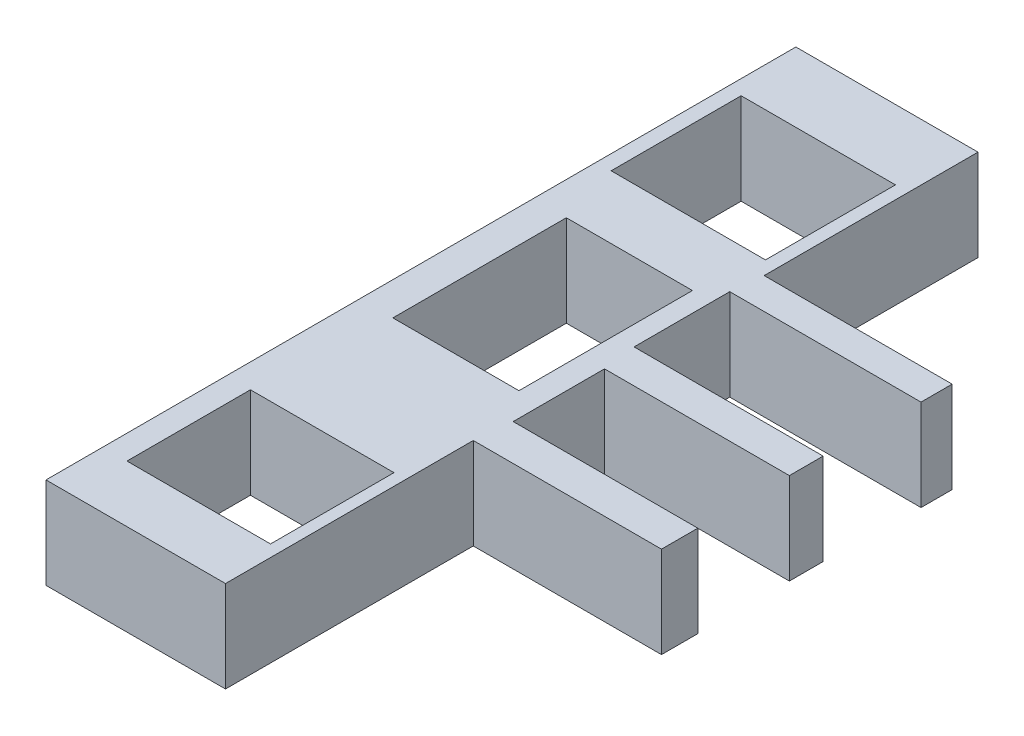
SolidWorks part; units mm, degrees
ref_plane "Front Plane" through (0, 0, 0) normal (0, 0, 1) x (1, 0, 0)
ref_plane "Top Plane" through (0, 0, 0) normal (0, 1, 0) x (1, 0, 0)
ref_plane "Right Plane" through (0, 0, 0) normal (1, 0, 0) x (0, 0, -1)
sketch "Sketch2" plane through (0, 0, 0) normal (0, 1, 0) x (1, 0, 0)
  line L0 (-27.9086, 57.4835) -> (-27.9086, -57.4249)
  line L1 (-27.9086, -57.4249) -> (-0.4053, -57.4249)
  line L2 (-0.4053, -57.4249) -> (-0.4053, -19.4557)
  line L3 (-0.4053, -19.4557) -> (28.4376, -19.4557)
  line L4 (28.4376, -19.4557) -> (28.4376, -13.8879)
  line L5 (28.4376, -13.8879) -> (0.1436, -13.8879)
  line L6 (0.1436, -13.8879) -> (0.1436, 0.106)
  line L7 (0.1436, 0.106) -> (28.4721, 0.106)
  line L8 (28.4721, 0.106) -> (28.4721, 5.2825)
  line L9 (28.4721, 5.2825) -> (-0.5019, 5.2825)
  line L10 (-0.5019, 5.2825) -> (-0.5019, 19.9459)
  line L11 (-0.5019, 19.9459) -> (28.8074, 19.9459)
  line L12 (28.8074, 19.9459) -> (28.8074, 24.7164)
  line L13 (28.8074, 24.7164) -> (0, 24.7164)
  line L14 (0, 24.7164) -> (0, 57.4835)
  line L15 (0, 57.4835) -> (-27.9086, 57.4835)
  line L17 (-25.6311, 26.8967) -> (-1.9799, 26.8967)
  line L18 (-25.6311, 26.8967) -> (-25.6311, 46.817)
  line L19 (-25.6311, 46.817) -> (-1.9799, 46.817)
  line L20 (-1.9799, 26.8967) -> (-1.9799, 46.817)
  line L21 (-22.833, 17.2364) -> (-3.5123, 17.2364)
  line L22 (-22.833, 17.2364) -> (-22.833, -9.3462)
  line L23 (-22.833, -9.3462) -> (-3.5123, -9.3462)
  line L24 (-3.5123, 17.2364) -> (-3.5123, -9.3462)
  line L25 (-24.2073, -29.7995) -> (-2.2073, -29.7995)
  line L26 (-24.2073, -29.7995) -> (-24.2073, -48.7204)
  line L27 (-24.2073, -48.7204) -> (-2.2073, -48.7204)
  line L28 (-2.2073, -29.7995) -> (-2.2073, -48.7204)
extrude "Boss-Extrude1" add sketch "Sketch2" along normal blind 14
